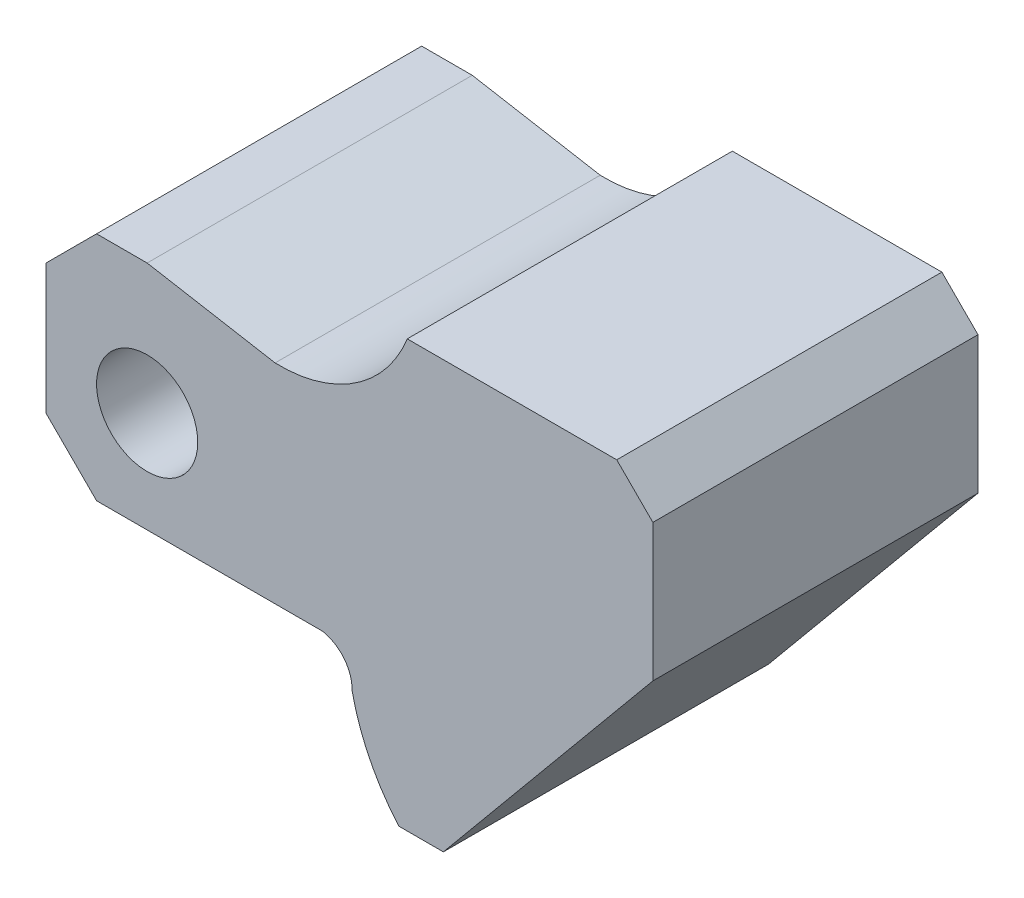
SolidWorks part; units mm, degrees
material "AISI 1020"
ref_plane "Plan de face" through (0, 0, 0) normal (0, 0, 1) x (1, 0, 0)
ref_plane "Plan de dessus" through (0, 0, 0) normal (0, 1, 0) x (1, 0, 0)
ref_plane "Plan de droite" through (0, 0, 0) normal (1, 0, 0) x (0, 0, -1)
sketch "Esquisse1" plane through (0, 0, 0) normal (0, 0, 1) x (1, 0, 0)
  line L15 (67.0555, 42.5858) -> (96.0555, 42.5858)
  line L16 (96.0555, 42.5858) -> (101.0555, 37.5858)
  line L17 (101.0555, 37.5858) -> (101.0555, 18.5858)
  line L20 (101.0555, 18.5858) -> (72.0555, -16.4142)
  line L24 (31.0555, 33.6764) -> (48.7651, 30.5538)
  line L25 (31.0555, 33.6764) -> (24.0555, 33.6764)
  line L26 (24.0555, 33.6764) -> (17.0555, 26.6764)
  line L27 (17.0555, 26.6764) -> (17.0555, 8.6764)
  line L28 (17.0555, 8.6764) -> (24.0555, 1.6764)
  line L30 (24.0555, 1.6764) -> (55.3502, 1.6764)
  line L31 (65.8895, -16.4142) -> (72.0555, -16.4142)
  arc A4 (67.0555, 42.5858) -> (48.7651, 30.5538) centre (49.3755, 49.544) cw
  arc A5 (55.3502, 1.6764) -> (59.4189, -3.3815) centre (54.421, -3.2365) cw
  arc A7 (59.4189, -3.3815) -> (65.8895, -16.4142) centre (87.7984, 2.5858) ccw
  point P7 (87.7984, 2.5858)
  dimension "D8" = 7
  dimension "D9" = 59
  dimension "D6" = 19
  dimension "D15" = 19
  dimension "D10" = 84
  dimension "D11" = 5
  dimension "D12" = 29
  dimension "D2" = 45
  dimension "D3" = 5
  dimension "D4" = 24
  dimension "D5" = 29
  dimension "D7" = 45
  dimension "D13" = 32
  dimension "D16" = 29
  dimension "D19" = 7
  dimension "D20" = 14
  dimension "D21" = 10
extrude "Boss.-Extru.1" add sketch "Esquisse1" along normal blind 45
sketch "Esquisse2" plane through (0, 0, 45) normal (0, 0, 1) x (1, 0, 0)
  line L0 (17.0555, 26.6764) -> (17.0555, 8.6764) construction
  line L1 (24.0555, 1.6764) -> (55.3502, 1.6764) construction
  circle A0 centre (31.0555, 15.6764) radius 7
  dimension "D1" = 14
  dimension "D2" = 14
  dimension "D3" = 14
extrude "Enlèv. mat.-Extru.1" cut sketch "Esquisse2" against normal blind 45
